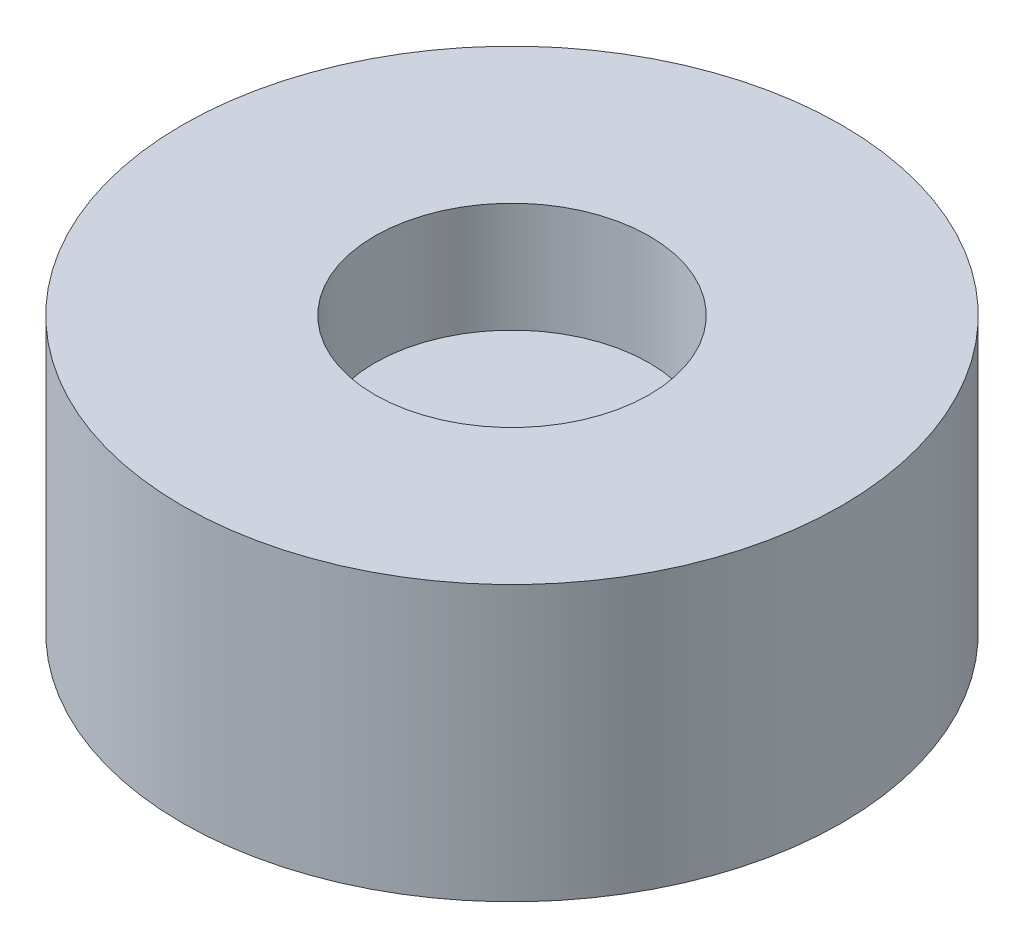
SolidWorks part; units mm, degrees
ref_plane "Front Plane" through (0, 0, 0) normal (0, 0, 1) x (1, 0, 0)
ref_plane "Top Plane" through (0, 0, 0) normal (0, 1, 0) x (1, 0, 0)
ref_plane "Right Plane" through (0, 0, 0) normal (1, 0, 0) x (0, 0, -1)
sketch "Sketch1" plane through (0, 0, 0) normal (0, 1, 0) x (1, 0, 0)
  circle A0 centre (0, 0) radius 6
  dimension "D1" = 12
extrude "Boss-Extrude1" add sketch "Sketch1" along normal blind 5
sketch "Sketch2" plane through (0, 5, 0) normal (0, 1, 0) x (1, 0, 0)
  circle A0 centre (0, 0) radius 2.5
  dimension "D1" = 5
extrude "Cut-Extrude1" cut sketch "Sketch2" against normal blind 2
sketch "Sketch3" plane through (0, 0, 0) normal (0, -1, 0) x (1, 0, 0)
  circle A0 centre (0, 0) radius 1
  dimension "D1" = 2
extrude "Cut-Extrude2" cut sketch "Sketch3" against normal blind 2
fillet "Fillet1" radius 1 1 edges at (0, 2, -1)
